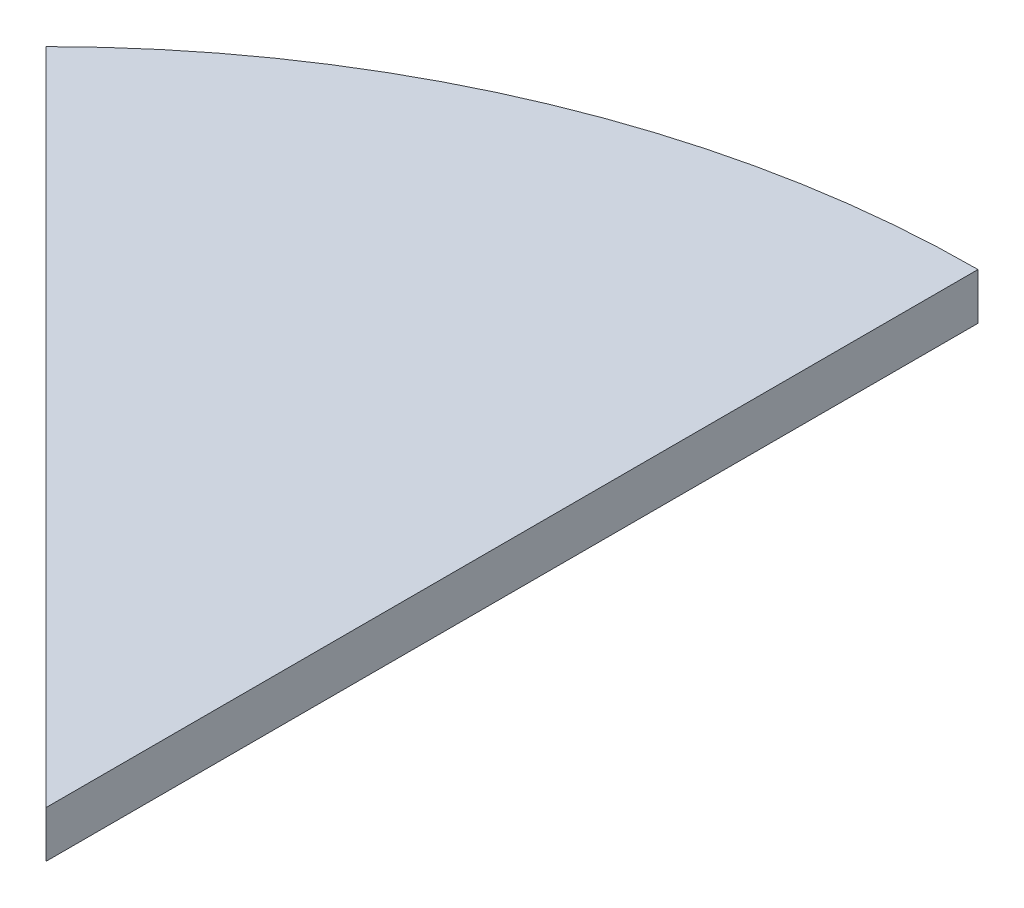
SolidWorks part; units mm, degrees
ref_plane "Front Plane" through (0, 0, 0) normal (0, 0, 1) x (1, 0, 0)
ref_plane "Top Plane" through (0, 0, 0) normal (0, 1, 0) x (1, 0, 0)
ref_plane "Right Plane" through (0, 0, 0) normal (1, 0, 0) x (0, 0, -1)
sketch "Sketch1" plane through (0, 0, 0) normal (0, 1, 0) x (1, 0, 0)
  line L0 (0, 400) -> (0, 0)
  line L1 (0, 0) -> (-282.8427, 282.8427)
  arc A0 (0, 400) -> (-282.8427, 282.8427) centre (0, 0) ccw
  dimension "D1" = 800
extrude "Extrude1" add sketch "Sketch1" along normal blind 20
